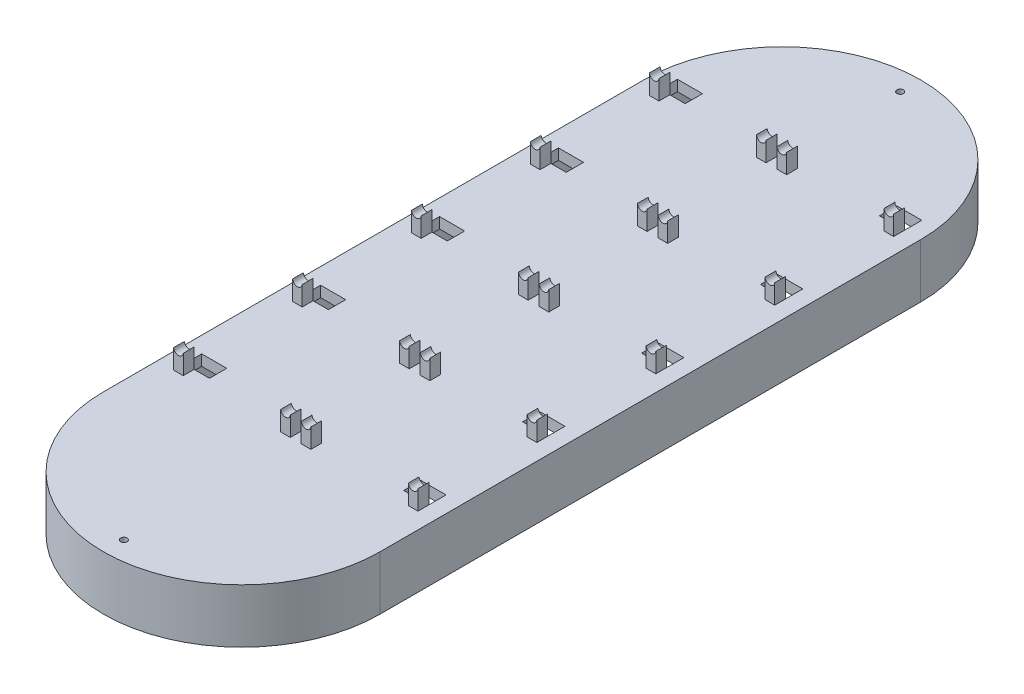
SolidWorks part; units mm, degrees
ref_plane "Front Plane" through (0, 0, 0) normal (0, 0, 1) x (1, 0, 0)
ref_plane "Top Plane" through (0, 0, 0) normal (0, 1, 0) x (1, 0, 0)
ref_plane "Right Plane" through (0, 0, 0) normal (1, 0, 0) x (0, 0, -1)
sketch "Sketch1" plane through (0, 0, 0) normal (0, 1, 0) x (1, 0, 0)
  line L0 (0, 0) -> (0, 250) construction
  line L1 (-64, 250) -> (-64, 0)
  line L2 (64, 250) -> (64, 0)
  arc A0 (-64, 0) -> (64, 0) centre (0, 0) ccw
  arc A1 (64, 250) -> (-64, 250) centre (0, 250) ccw
  dimension "D1" = 128
  dimension "D2" = 128
  dimension "D3" = 250
extrude "Boss-Extrude1" add sketch "Sketch1" along normal blind 5
sketch "Sketch2" plane through (0, 5, 0) normal (0, 1, 0) x (1, 0, 0)
  line L0 (0, 0) -> (0, 25)
  line L1 (0, 30) -> (0, 80)
  line L2 (9, 25) -> (-9, 25)
  line L3 (0, 25) -> (0, 30)
  line L4 (9, 30) -> (-9, 30)
  line L5 (-9, 25) -> (-9, 30)
  line L6 (0, 85) -> (0, 135)
  line L7 (9, 80) -> (-9, 80)
  line L8 (0, 80) -> (0, 85)
  line L9 (9, 85) -> (-9, 85)
  line L10 (-9, 80) -> (-9, 85)
  line L11 (0, 140) -> (0, 190)
  line L12 (9, 135) -> (-9, 135)
  line L13 (0, 135) -> (0, 140)
  line L14 (9, 140) -> (-9, 140)
  line L15 (-9, 135) -> (-9, 140)
  line L16 (0, 195) -> (0, 245)
  line L17 (9, 190) -> (-9, 190)
  line L18 (0, 190) -> (0, 195)
  line L19 (9, 195) -> (-9, 195)
  line L20 (-9, 190) -> (-9, 195)
  line L21 (-9, 30) -> (-49, 30)
  line L22 (9, 245) -> (-9, 245)
  line L23 (0, 245) -> (0, 250)
  line L24 (9, 250) -> (-9, 250)
  line L25 (-9, 245) -> (-9, 250)
  line L26 (-9, 85) -> (-49, 85)
  line L27 (-49, 30) -> (-58, 30)
  line L28 (-49, 30) -> (-49, 25)
  line L29 (-49, 25) -> (-58, 25)
  line L30 (-58, 30) -> (-58, 25)
  line L31 (-9, 140) -> (-49, 140)
  line L32 (-49, 85) -> (-58, 85)
  line L33 (-49, 85) -> (-49, 80)
  line L34 (-49, 80) -> (-58, 80)
  line L35 (-58, 85) -> (-58, 80)
  line L36 (-9, 195) -> (-49, 195)
  line L37 (-49, 140) -> (-58, 140)
  line L38 (-49, 140) -> (-49, 135)
  line L39 (-49, 135) -> (-58, 135)
  line L40 (-58, 140) -> (-58, 135)
  line L41 (-9, 250) -> (-49, 250)
  line L42 (-49, 195) -> (-58, 195)
  line L43 (-49, 195) -> (-49, 190)
  line L44 (-49, 190) -> (-58, 190)
  line L45 (-58, 195) -> (-58, 190)
  line L46 (9, 245) -> (9, 250)
  line L47 (-49, 250) -> (-58, 250)
  line L48 (-49, 250) -> (-49, 245)
  line L49 (-49, 245) -> (-58, 245)
  line L50 (-58, 250) -> (-58, 245)
  line L51 (49, 245) -> (58, 245)
  line L52 (58, 250) -> (58, 245)
  line L53 (49, 250) -> (58, 250)
  line L54 (49, 250) -> (49, 245)
  line L55 (9, 135) -> (9, 140)
  line L56 (49, 135) -> (58, 135)
  line L57 (58, 140) -> (58, 135)
  line L58 (49, 140) -> (58, 140)
  line L59 (49, 140) -> (49, 135)
  line L60 (9, 190) -> (9, 195)
  line L61 (49, 190) -> (58, 190)
  line L62 (58, 195) -> (58, 190)
  line L63 (49, 195) -> (58, 195)
  line L64 (49, 195) -> (49, 190)
  line L65 (9, 80) -> (9, 85)
  line L66 (49, 80) -> (58, 80)
  line L67 (58, 85) -> (58, 80)
  line L68 (49, 85) -> (58, 85)
  line L69 (49, 85) -> (49, 80)
  line L70 (49, 25) -> (58, 25)
  line L71 (58, 30) -> (58, 25)
  line L72 (49, 30) -> (58, 30)
  line L73 (49, 30) -> (49, 25)
  line L74 (9, 25) -> (9, 30)
  dimension "D1" = 25
  dimension "D2" = 9
  dimension "D3" = 5
  dimension "D4" = 50
  dimension "D5" = 9
  dimension "D6" = 5
  dimension "D7" = 50
  dimension "D8" = 9
  dimension "D9" = 5
  dimension "D10" = 50
  dimension "D11" = 9
  dimension "D12" = 5
  dimension "D13" = 50
  dimension "D14" = 9
  dimension "D15" = 5
  dimension "D16" = 40
  dimension "D17" = 9
extrude "Boss-Extrude2" add sketch "Sketch2" along normal blind 9 contours L2 L74 L4 L3 | L5 L2 L3 L4 | L27 L30 L29 L28 | L72 L73 L70 L71 | L68 L69 L66 L67 | L7 L65 L9 L8 | L10 L7 L8 L9 | L32 L35 L34 L33 | L37 L40 L39 L38 | L15 L12 L13 L14 | L12 L55 L14 L13 | L58 L59 L56 L57 | L63 L64 L61 L62 | L42 L45 L44 L43 | L47 L50 L49 L48 | L25 L22 L23 L24 | L22 L46 L24 L23 | L53 L54 L51 L52 | L20 L17 L60 L19
sketch "Sketch3" plane through (0, 0, -25) normal (0, 0, 1) x (1, 0, 0)
  line L0 (-54.2639, 12) -> (-54.2639, 5)
  line L1 (-49, 14) -> (-58, 14) construction
  line L3 (-49, 5) -> (-58, 5) construction
  line L4 (-52.0279, 14) -> (-52.0279, 5)
  line L5 (-52.0279, 5) -> (-49, 5)
  line L6 (-49, 5) -> (-49, 14)
  line L7 (-49, 14) -> (-52.0279, 14)
  line L8 (-56.5, 14) -> (-56.5, 5)
  line L9 (-56.5, 5) -> (-58, 5)
  line L10 (-58, 5) -> (-58, 14)
  line L11 (-58, 14) -> (-56.5, 14)
  line L12 (-9, 14) -> (-4.7639, 14)
  line L13 (9, 14) -> (-9, 14) construction
  line L14 (-4.7639, 14) -> (-4.7639, 5) construction
  line L15 (9, 5) -> (-9, 5) construction
  line L16 (-4.7639, 12) -> (-4.7639, 5)
  line L17 (-7, 14) -> (-7, 5)
  line L18 (-7, 5) -> (-9, 5)
  line L19 (-9, 5) -> (-9, 14)
  line L20 (-9, 14) -> (-7, 14)
  line L21 (-2.5279, 14) -> (-2.5279, 5)
  line L22 (64, 5) -> (-64, 5) construction
  line L23 (0, 14) -> (0, 5) construction
  line L24 (-2.5279, 14) -> (2.5279, 14)
  line L25 (-2.5279, 5) -> (2.5279, 5)
  line L26 (49, 5) -> (49, 14)
  line L27 (52.0279, 5) -> (49, 5)
  line L28 (52.0279, 14) -> (52.0279, 5)
  line L29 (49, 14) -> (52.0279, 14)
  line L30 (58, 5) -> (58, 14)
  line L31 (56.5, 5) -> (58, 5)
  line L32 (56.5, 14) -> (56.5, 5)
  line L33 (58, 14) -> (56.5, 14)
  line L34 (2.5279, 14) -> (2.5279, 5)
  line L35 (9, 5) -> (9, 14)
  line L36 (7, 5) -> (9, 5)
  line L37 (7, 14) -> (7, 5)
  line L38 (9, 14) -> (7, 14)
  circle A0 centre (-54.2639, 14.25) radius 2.25
  circle A1 centre (-4.7639, 14.25) radius 2.25
  circle A2 centre (54.2639, 14.25) radius 2.25
  circle A3 centre (4.7639, 14.25) radius 2.25
  dimension "D1" = 4.5
  dimension "D4" = 4.5
  dimension "D2" = 7
  dimension "D3" = 2
  dimension "D5" = 7
  dimension "D6" = 1.5
extrude "Cut-Extrude1" cut sketch "Sketch3" against normal blind 228
sketch "Sketch4" plane through (0, 0, 0) normal (0, -1, 0) x (1, 0, 0)
  line L0 (-64, 0) -> (-64, -250)
  line L1 (64, -250) -> (64, 0)
  line L2 (-59, 0) -> (-59, -250)
  line L3 (59, -250) -> (59, 0)
  arc A0 (64, 0) -> (-64, 0) centre (0, 0) ccw
  arc A1 (-64, -250) -> (64, -250) centre (0, -250) ccw
  arc A2 (59, 0) -> (-59, 0) centre (0, 0) ccw
  arc A3 (-59, -250) -> (59, -250) centre (0, -250) ccw
  dimension "D1" = 5
extrude "Boss-Extrude3" add sketch "Sketch4" along normal blind 20
sketch "Sketch5" plane through (0, 5, 0) normal (0, 1, 0) x (1, 0, 0)
  line L0 (0, 0) -> (0, -26.8786) construction
  line L21 (-56.5, 250) -> (-44.9161, 250)
  line L22 (-56.5, 250) -> (-56.5, 258)
  line L23 (-56.5, 258) -> (-44.9161, 258)
  line L24 (-44.9161, 250) -> (-44.9161, 258)
  line L25 (-56.5, 195) -> (-44.9161, 195)
  line L26 (-56.5, 195) -> (-56.5, 203)
  line L27 (-56.5, 203) -> (-44.9161, 203)
  line L28 (-44.9161, 195) -> (-44.9161, 203)
  line L29 (-56.5, 140) -> (-44.9161, 140)
  line L30 (-56.5, 140) -> (-56.5, 148)
  line L31 (-56.5, 148) -> (-44.9161, 148)
  line L32 (-44.9161, 140) -> (-44.9161, 148)
  line L33 (-56.5, 85) -> (-44.9161, 85)
  line L34 (-56.5, 85) -> (-56.5, 93)
  line L35 (-56.5, 93) -> (-44.9161, 93)
  line L36 (-44.9161, 85) -> (-44.9161, 93)
  line L37 (-56.5, 30) -> (-44.9161, 30)
  line L38 (-56.5, 30) -> (-56.5, 38)
  line L39 (-56.5, 38) -> (-44.9161, 38)
  line L40 (-44.9161, 30) -> (-44.9161, 38)
  line L41 (56.5, 148) -> (44.9161, 148)
  line L42 (44.9161, 140) -> (44.9161, 148)
  line L43 (56.5, 140) -> (44.9161, 140)
  line L44 (56.5, 140) -> (56.5, 148)
  line L45 (56.5, 203) -> (44.9161, 203)
  line L46 (44.9161, 195) -> (44.9161, 203)
  line L47 (56.5, 195) -> (44.9161, 195)
  line L48 (56.5, 195) -> (56.5, 203)
  line L49 (56.5, 258) -> (44.9161, 258)
  line L50 (44.9161, 250) -> (44.9161, 258)
  line L51 (56.5, 250) -> (44.9161, 250)
  line L52 (56.5, 250) -> (56.5, 258)
  line L53 (56.5, 93) -> (44.9161, 93)
  line L54 (44.9161, 85) -> (44.9161, 93)
  line L55 (56.5, 85) -> (44.9161, 85)
  line L56 (56.5, 85) -> (56.5, 93)
  line L57 (56.5, 38) -> (44.9161, 38)
  line L58 (44.9161, 30) -> (44.9161, 38)
  line L59 (56.5, 30) -> (44.9161, 30)
  line L60 (56.5, 30) -> (56.5, 38)
  dimension "D2" = 8
  dimension "D3" = 8
  dimension "D4" = 8
  dimension "D9" = 8
  dimension "D10" = 8
extrude "Cut-Extrude3" cut sketch "Sketch5" against normal blind 20
sketch "Sketch6" plane through (0, 0, 0) normal (0, -1, 0) x (1, 0, 0)
  line L0 (0, -309) -> (0, 59) construction
  arc A0 (-59, -250) -> (59, -250) centre (0, -250) ccw construction
  arc A1 (59, 0) -> (-59, 0) centre (0, 0) ccw construction
  circle A2 centre (0, 54.4717) radius 1.5
  circle A3 centre (0, -304.5136) radius 1.5
  circle A4 centre (0, 54.4717) radius 4.5
  circle A5 centre (0, -304.5136) radius 4.5
  point P10 (0, -304.5136)
  dimension "D1" = 3
  dimension "D2" = 3
  dimension "D3" = 3
  dimension "D4" = 3
extrude "Cut-Extrude5" cut sketch "Sketch6" against normal blind 25 contours A3 | A2
